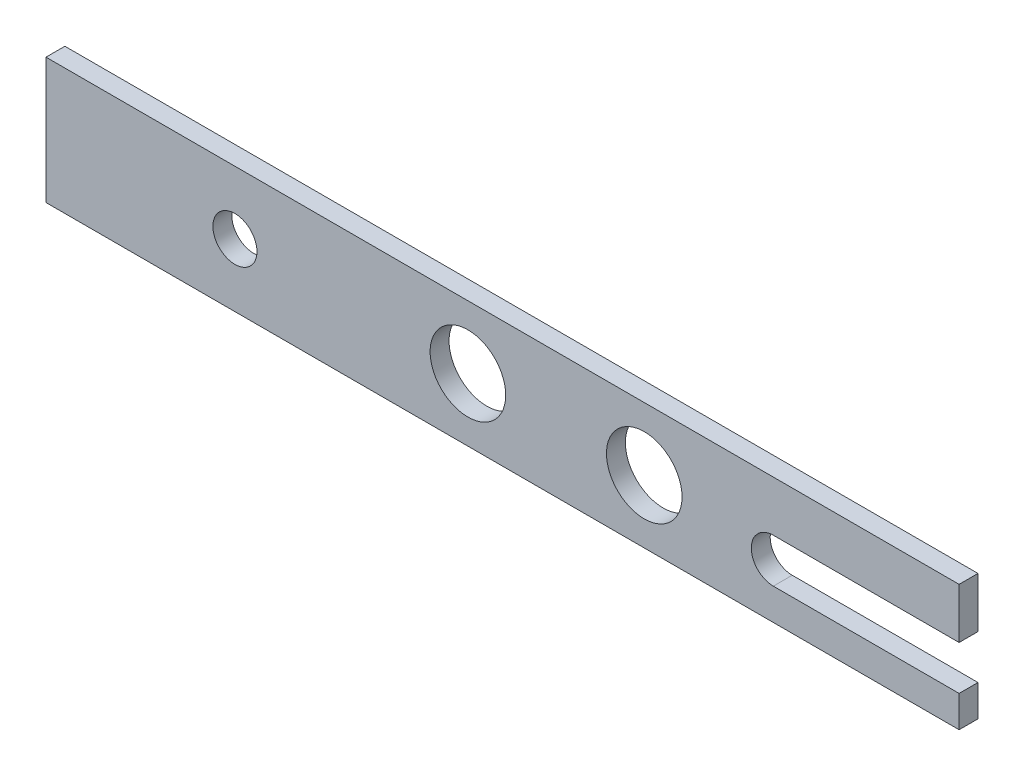
SolidWorks part; units mm, degrees
ref_plane "Front Plane" through (0, 0, 0) normal (0, 0, 1) x (1, 0, 0)
ref_plane "Top Plane" through (0, 0, 0) normal (0, 1, 0) x (1, 0, 0)
ref_plane "Right Plane" through (0, 0, 0) normal (1, 0, 0) x (0, 0, -1)
sketch "Sketch1" plane through (0, 0, 0) normal (0, 0, 1) x (1, 0, 0)
  line L1 (0, 0) -> (145, 0)
  line L2 (0, 0) -> (0, 20)
  line L3 (0, 20) -> (145, 20)
  line L4 (145, 0) -> (145, 20)
  line L5 (145, 12) -> (115.5, 12)
  line L6 (145, 12) -> (145, 5)
  line L7 (145, 5) -> (115.5, 5)
  circle A0 centre (30, 10) radius 3.5
  circle A3 centre (67, 10) radius 6
  circle A4 centre (95, 10) radius 6
  arc A7 (115.5, 5) -> (115.5, 12) centre (115.5, 8.5) cw
  point P19 (0, 10)
  dimension "D6" = 7
  dimension "D7" = 115
  dimension "D9" = 12
  dimension "D10" = 12
  dimension "D11" = 78
  dimension "D12" = 50
  dimension "D3" = 29.5
  dimension "D1" = 20
  dimension "D2" = 145
  dimension "D4" = 7
  dimension "D5" = 8
extrude "Boss-Extrude1" add sketch "Sketch1" along normal blind 3 contours L7 A7 L5 L4 L3 L2 L1 A4 A3 A0
